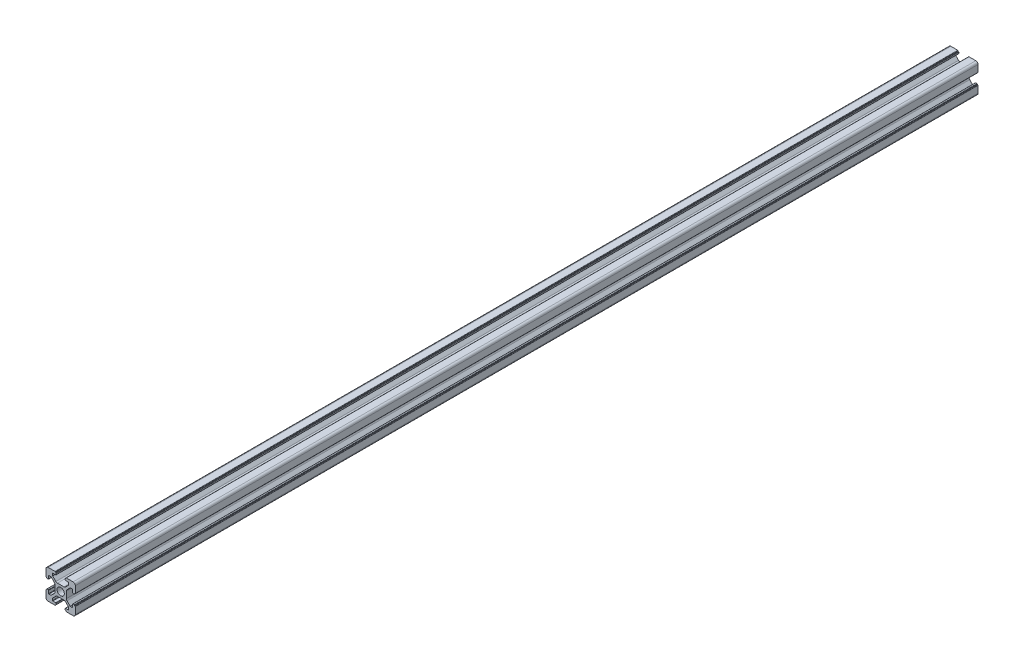
SolidWorks part; units mm, degrees
material "1060 Alloy"
ref_plane "前视基准面" through (0, 0, 0) normal (0, 0, 1) x (1, 0, 0)
ref_plane "上视基准面" through (0, 0, 0) normal (0, 1, 0) x (1, 0, 0)
ref_plane "右视基准面" through (0, 0, 0) normal (1, 0, 0) x (0, 0, -1)
sketch "草图1" plane through (0, 0, 0) normal (0, 0, 1) x (1, 0, 0)
  line L0 (0, 0) -> (0, 5.5) construction
  line L1 (-8.5023, -10.0023) -> (-3.85, -10.0023)
  line L2 (-10.0023, -8.5023) -> (-10.0023, -3.85)
  line L3 (-8.5023, 10.0023) -> (-3.85, 10.0023)
  line L4 (10.0023, -8.5023) -> (10.0023, -3.85)
  line L5 (-10.0023, -10.0023) -> (10.0023, 10.0023) construction
  line L6 (-10.0023, 10.0023) -> (10.0023, -10.0023) construction
  line L7 (-2.218, -3.9) -> (2.218, -3.9)
  line L8 (-3.9, -2.218) -> (-3.9, 2.218)
  line L9 (-2.218, 3.9) -> (2.218, 3.9)
  line L10 (3.9, -2.218) -> (3.9, 2.218)
  line L11 (-3.9, -3.9) -> (3.9, 3.9) construction
  line L12 (-3.9, 3.9) -> (3.9, -3.9) construction
  line L13 (-5.25, -8.2) -> (-3.35, -8.2)
  line L14 (-8.2, -5.25) -> (-8.2, -3.35)
  line L15 (-5.25, 8.2) -> (-3.35, 8.2)
  line L16 (8.2, -5.25) -> (8.2, -3.35)
  line L17 (-8.2, -8.2) -> (8.2, 8.2) construction
  line L18 (-8.2, 8.2) -> (8.2, -8.2) construction
  line L19 (-7.95, 5.5) -> (-6.6642, 5.5)
  line L20 (0, 0) -> (5.5, 0) construction
  line L23 (-5.5, 7.95) -> (-5.5, 6.6642)
  line L26 (0, 0) -> (-0.5303, 0.5303)
  line L27 (3.2787, 4.3393) -> (5.4268, 6.4874)
  line L28 (0, 0) -> (0.5303, -0.5303)
  line L29 (5.5, 6.6642) -> (5.5, 7.95)
  line L30 (4.3393, 3.2787) -> (6.4874, 5.4268)
  line L31 (6.6642, 5.5) -> (7.95, 5.5)
  line L32 (4.3393, -3.2787) -> (6.4874, -5.4268)
  line L33 (3.2787, -4.3393) -> (5.4268, -6.4874)
  line L34 (-3.2787, -4.3393) -> (-5.4268, -6.4874)
  line L35 (-4.3393, -3.2787) -> (-6.4874, -5.4268)
  line L36 (-4.3393, 3.2787) -> (-6.4874, 5.4268)
  line L37 (-3.2787, 4.3393) -> (-5.4268, 6.4874)
  line L38 (3.1, -8.45) -> (3.1, -9.2523)
  line L39 (8.45, 3.1) -> (9.2523, 3.1)
  line L40 (-5.5, -6.6642) -> (-5.5, -7.95)
  line L41 (-6.6642, -5.5) -> (-7.95, -5.5)
  line L42 (5.5, -6.6642) -> (5.5, -7.95)
  line L43 (6.6642, -5.5) -> (7.95, -5.5)
  line L44 (9.2523, -3.1) -> (8.45, -3.1)
  line L46 (10.0023, 3.85) -> (10.0023, 8.5023)
  line L47 (8.2, 3.35) -> (8.2, 5.25)
  line L48 (-3.1, -9.2523) -> (-3.1, -8.45)
  line L49 (-8.45, -3.1) -> (-9.2523, -3.1)
  line L50 (-9.2523, 3.1) -> (-8.45, 3.1)
  line L51 (-3.1, 8.45) -> (-3.1, 9.2523)
  line L52 (3.1, 9.2523) -> (3.1, 8.45)
  line L53 (3.85, 10.0023) -> (8.5023, 10.0023)
  line L54 (3.35, 8.2) -> (5.25, 8.2)
  line L55 (-10.0023, 3.85) -> (-10.0023, 8.5023)
  line L56 (-8.2, 3.35) -> (-8.2, 5.25)
  line L57 (3.35, -8.2) -> (5.25, -8.2)
  line L58 (3.85, -10.0023) -> (8.5023, -10.0023)
  line L59 (9.7523, -3.6) -> (9.5023, -3.6)
  line L61 (9.7523, 3.6) -> (9.5023, 3.6)
  line L62 (9.5023, -3.6) -> (9.5023, -3.35)
  line L63 (3.6, -9.7523) -> (3.6, -9.5023)
  line L64 (3.35, -9.5023) -> (3.6, -9.5023)
  line L65 (9.5023, 3.35) -> (9.5023, 3.6)
  line L66 (-3.6, -9.5023) -> (-3.35, -9.5023)
  line L67 (-3.6, -9.7523) -> (-3.6, -9.5023)
  line L68 (-9.7523, -3.6) -> (-9.5023, -3.6)
  line L69 (-9.5023, -3.35) -> (-9.5023, -3.6)
  line L70 (-9.5023, 3.6) -> (-9.5023, 3.35)
  line L71 (-9.7523, 3.6) -> (-9.5023, 3.6)
  line L72 (-3.6, 9.7523) -> (-3.6, 9.5023)
  line L73 (-3.35, 9.5023) -> (-3.6, 9.5023)
  line L74 (3.6, 9.5023) -> (3.35, 9.5023)
  line L75 (3.6, 9.7523) -> (3.6, 9.5023)
  circle A0 centre (0, 0) radius 2.5
  arc A1 (10.0023, 8.5023) -> (8.5023, 10.0023) centre (8.5023, 8.5023) ccw
  arc A2 (8.5023, -10.0023) -> (10.0023, -8.5023) centre (8.5023, -8.5023) ccw
  arc A3 (-10.0023, -8.5023) -> (-8.5023, -10.0023) centre (-8.5023, -8.5023) ccw
  arc A4 (-10.0023, 8.5023) -> (-8.5023, 10.0023) centre (-8.5023, 8.5023) cw
  arc A5 (-9.5023, -3.35) -> (-9.2523, -3.1) centre (-9.2523, -3.35) cw
  arc A6 (-9.7523, -3.6) -> (-10.0023, -3.85) centre (-9.7523, -3.85) ccw
  arc A7 (-8.45, -3.1) -> (-8.2, -3.35) centre (-8.45, -3.35) cw
  arc A8 (-7.95, -5.5) -> (-8.2, -5.25) centre (-7.95, -5.25) cw
  arc A9 (-6.4874, -5.4268) -> (-6.6642, -5.5) centre (-6.6642, -5.25) cw
  arc A10 (-5.4268, -6.4874) -> (-5.5, -6.6642) centre (-5.25, -6.6642) ccw
  arc A11 (-5.5, -7.95) -> (-5.25, -8.2) centre (-5.25, -7.95) ccw
  arc A12 (-3.6, -9.7523) -> (-3.85, -10.0023) centre (-3.85, -9.7523) cw
  arc A13 (-3.35, -9.5023) -> (-3.1, -9.2523) centre (-3.35, -9.2523) ccw
  arc A14 (-3.1, -8.45) -> (-3.35, -8.2) centre (-3.35, -8.45) ccw
  arc A15 (3.1, -8.45) -> (3.35, -8.2) centre (3.35, -8.45) cw
  arc A16 (5.5, -7.95) -> (5.25, -8.2) centre (5.25, -7.95) cw
  arc A17 (5.4268, -6.4874) -> (5.5, -6.6642) centre (5.25, -6.6642) cw
  arc A18 (6.4874, -5.4268) -> (6.6642, -5.5) centre (6.6642, -5.25) ccw
  arc A19 (7.95, -5.5) -> (8.2, -5.25) centre (7.95, -5.25) ccw
  arc A20 (8.45, -3.1) -> (8.2, -3.35) centre (8.45, -3.35) ccw
  arc A21 (9.5023, -3.35) -> (9.2523, -3.1) centre (9.2523, -3.35) ccw
  arc A22 (9.7523, -3.6) -> (10.0023, -3.85) centre (9.7523, -3.85) cw
  arc A23 (3.35, -9.5023) -> (3.1, -9.2523) centre (3.35, -9.2523) cw
  arc A24 (3.6, -9.7523) -> (3.85, -10.0023) centre (3.85, -9.7523) ccw
  arc A25 (7.95, 5.5) -> (8.2, 5.25) centre (7.95, 5.25) cw
  arc A26 (8.2, 3.35) -> (8.45, 3.1) centre (8.45, 3.35) ccw
  arc A27 (9.5023, 3.35) -> (9.2523, 3.1) centre (9.2523, 3.35) cw
  arc A28 (9.7523, 3.6) -> (10.0023, 3.85) centre (9.7523, 3.85) ccw
  arc A29 (6.6642, 5.5) -> (6.4874, 5.4268) centre (6.6642, 5.25) ccw
  arc A30 (5.4268, 6.4874) -> (5.5, 6.6642) centre (5.25, 6.6642) ccw
  arc A31 (5.5, 7.95) -> (5.25, 8.2) centre (5.25, 7.95) ccw
  arc A32 (3.1, 8.45) -> (3.35, 8.2) centre (3.35, 8.45) ccw
  arc A33 (3.6, 9.7523) -> (3.85, 10.0023) centre (3.85, 9.7523) cw
  arc A34 (3.35, 9.5023) -> (3.1, 9.2523) centre (3.35, 9.2523) ccw
  arc A35 (-9.7523, 3.6) -> (-10.0023, 3.85) centre (-9.7523, 3.85) cw
  arc A36 (-9.5023, 3.35) -> (-9.2523, 3.1) centre (-9.2523, 3.35) ccw
  arc A37 (-8.45, 3.1) -> (-8.2, 3.35) centre (-8.45, 3.35) ccw
  arc A38 (-8.2, 5.25) -> (-7.95, 5.5) centre (-7.95, 5.25) cw
  arc A39 (-6.4874, 5.4268) -> (-6.6642, 5.5) centre (-6.6642, 5.25) ccw
  arc A40 (-5.4268, 6.4874) -> (-5.5, 6.6642) centre (-5.25, 6.6642) cw
  arc A41 (-5.5, 7.95) -> (-5.25, 8.2) centre (-5.25, 7.95) cw
  arc A42 (-3.1, 8.45) -> (-3.35, 8.2) centre (-3.35, 8.45) cw
  arc A43 (-3.1, 9.2523) -> (-3.35, 9.5023) centre (-3.35, 9.2523) ccw
  arc A44 (-3.6, 9.7523) -> (-3.85, 10.0023) centre (-3.85, 9.7523) ccw
  arc A45 (-4.3393, 3.2787) -> (-3.9, 2.218) centre (-5.4, 2.218) cw
  arc A46 (-3.2787, 4.3393) -> (-2.218, 3.9) centre (-2.218, 5.4) ccw
  arc A47 (3.2787, 4.3393) -> (2.218, 3.9) centre (2.218, 5.4) cw
  arc A48 (4.3393, 3.2787) -> (3.9, 2.218) centre (5.4, 2.218) ccw
  arc A49 (4.3393, -3.2787) -> (3.9, -2.218) centre (5.4, -2.218) cw
  arc A50 (3.2787, -4.3393) -> (2.218, -3.9) centre (2.218, -5.4) ccw
  arc A51 (-4.3393, -3.2787) -> (-3.9, -2.218) centre (-5.4, -2.218) ccw
  arc A52 (-2.218, -3.9) -> (-3.2787, -4.3393) centre (-2.218, -5.4) ccw
  point P0 (0, 0)
  point P7 (10.0023, 0)
  point P62 (0, 0)
  point P76 (0, 0)
  point P92 (-8.2, -5.5)
  point P99 (0, 0)
  point P106 (-5.5, -8.2)
  point P117 (5.5, -8.2)
  point P124 (8.2, -5.5)
  point P137 (8.2, 5.5)
  point P140 (8.2, 3.1)
  point P147 (6.5607, 5.5)
  point P152 (5.5, 8.2)
  point P167 (-8.2, 5.5)
  point P174 (-5.5, 8.2)
  dimension "D1" = 1.5
  dimension "D5" = 0.25
  dimension "D6" = 1.5
  dimension "D2" = 4
  dimension "D3" = 4
  dimension "D4" = 4
extrude "凸台-拉伸1" add sketch "草图1" along normal blind 616 contours A52 L7 A50 L33 A17 L42 A16 L57 A15 L38 A23 L64 L63 A24 L58 A2 L4 A22 L59 L62 A21 L44 A20 L16 A19 L43 A18 L32 A49 L10 A48 L30 A29 L31 A25 L47 A26 L39 A27 L65 L61 A28 L46 A1 L53 A33 L75 L74 A34 L52 A32
ref_plane "Plane1" through (0, 0, 308) normal (0, 0, 1) x (1, 0, 0)
